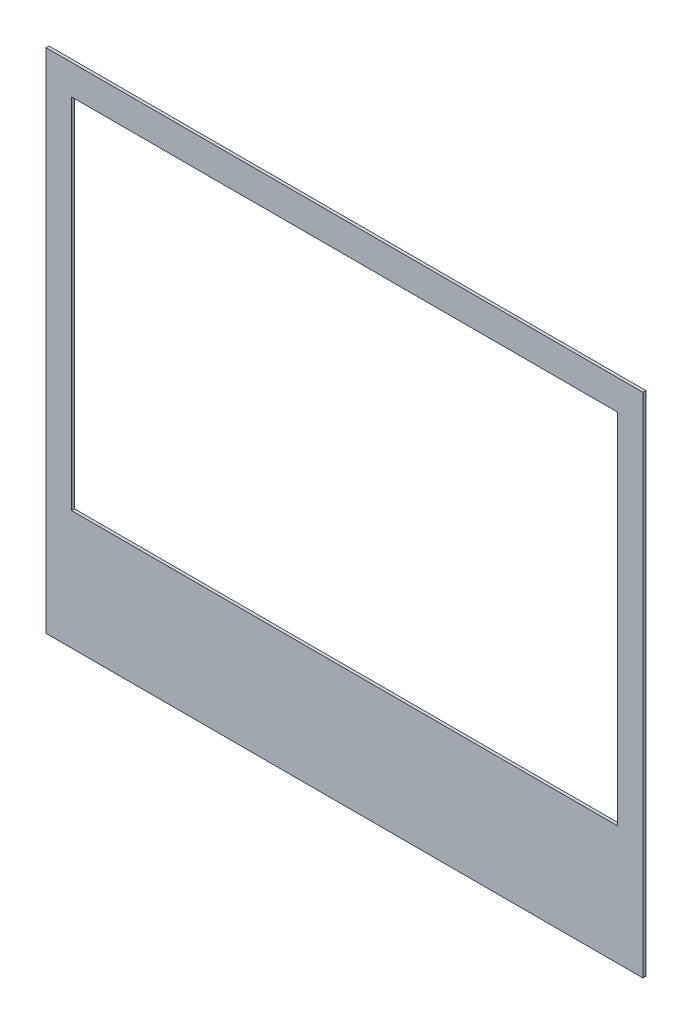
SolidWorks part; units mm, degrees
material "PET"
ref_plane "Plano frontal" through (0, 0, 0) normal (0, 0, 1) x (1, 0, 0)
ref_plane "Plano superior" through (0, 0, 0) normal (0, 1, 0) x (1, 0, 0)
ref_plane "Plano direito" through (0, 0, 0) normal (1, 0, 0) x (0, 0, -1)
sketch "Esboço1" plane through (0, 0, 0) normal (0, 0, 1) x (1, 0, 0)
  line L0 (39.98, 32.89) -> (39.98, -0.01) construction
  line L1 (0, 0) -> (39.98, 0)
  line L2 (0, 0) -> (0, 33.98)
  line L3 (0, 33.98) -> (39.98, 33.98)
  line L4 (39.98, 0) -> (39.98, 33.98)
  line L5 (38.99, 33.98) -> (0.99, 33.98) construction
  line L7 (1.7, 31.98) -> (38.28, 31.98)
  line L8 (1.7, 31.98) -> (1.7, 7.98)
  line L9 (1.7, 7.98) -> (38.28, 7.98)
  line L10 (38.28, 31.98) -> (38.28, 7.98)
  dimension "D1" = 1.7
  dimension "D2" = 1.7
  dimension "D3" = 2
  dimension "D4" = 24
extrude "Ressalto-extrusão1" add sketch "Esboço1" along normal blind 0.2
